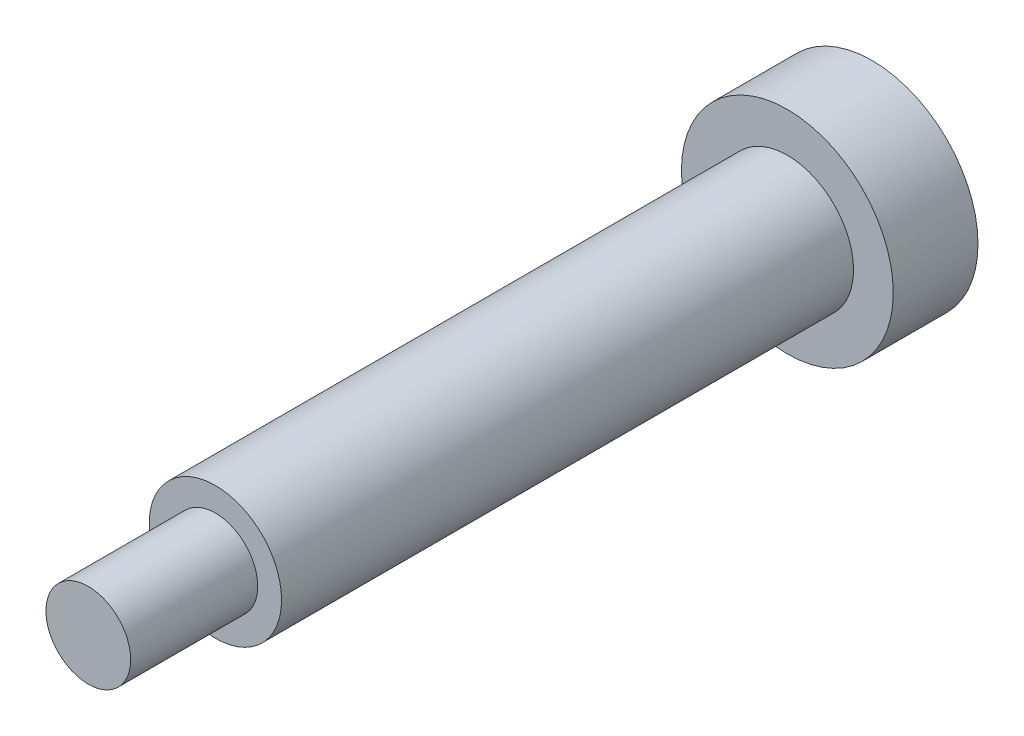
SolidWorks part; units mm, degrees
ref_plane "Front Plane" through (0, 0, 0) normal (0, 0, 1) x (1, 0, 0)
ref_plane "Top Plane" through (0, 0, 0) normal (0, 1, 0) x (1, 0, 0)
ref_plane "Right Plane" through (0, 0, 0) normal (1, 0, 0) x (0, 0, -1)
sketch "Sketch1" plane through (0, 0, 0) normal (0, 0, 1) x (1, 0, 0)
  circle A0 centre (0, 0) radius 5
  dimension "D1" = 10
extrude "Boss-Extrude1" add sketch "Sketch1" along normal blind 4
sketch "Sketch2" plane through (0, 0, 4) normal (0, 0, 1) x (1, 0, 0)
  circle A0 centre (0, 0) radius 3.125
  dimension "D1" = 6.25
extrude "Boss-Extrude2" add sketch "Sketch2" along normal blind 27
sketch "Sketch3" plane through (0, 0, 31) normal (0, 0, 1) x (1, 0, 0)
  circle A0 centre (0, 0) radius 2
  dimension "D1" = 4
extrude "Boss-Extrude3" add sketch "Sketch3" along normal blind 6
